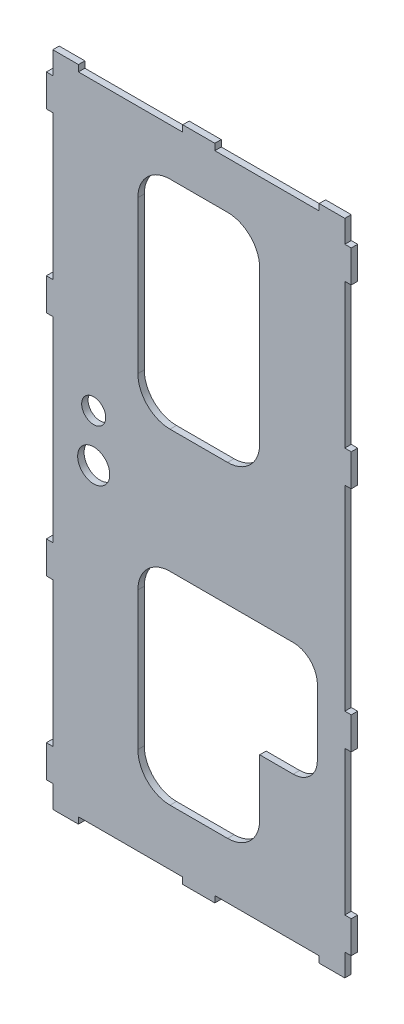
SolidWorks part; units mm, degrees
ref_plane "Front Plane" through (0, 0, 0) normal (0, 0, 1) x (1, 0, 0)
ref_plane "Top Plane" through (0, 0, 0) normal (0, 1, 0) x (1, 0, 0)
ref_plane "Right Plane" through (0, 0, 0) normal (1, 0, 0) x (0, 0, -1)
sketch "Sketch1" plane through (0, 0, 0) normal (0, 0, 1) x (1, 0, 0)
  line L0 (0, 263.7647) -> (0, -233.1278) construction
  line L2 (-75, -201) -> (-10, -201)
  line L3 (-95, -191) -> (-95, -171)
  line L5 (95, -191) -> (95, -171)
  line L10 (-95, 191) -> (-91, 191)
  line L11 (-91, 171) -> (-95, 171)
  line L12 (-95, 81) -> (-91, 81)
  line L13 (-91, 61) -> (-95, 61)
  line L14 (-95, -61) -> (-91, -61)
  line L15 (-91, -81) -> (-95, -81)
  line L16 (-95, -171) -> (-91, -171)
  line L17 (-91, -191) -> (-95, -191)
  line L18 (-91, 191) -> (-91, 205)
  line L19 (-95, 171) -> (-95, 191)
  line L20 (-91, 81) -> (-91, 171)
  line L21 (-95, 61) -> (-95, 81)
  line L22 (-91, -61) -> (-91, 61)
  line L23 (-95, -81) -> (-95, -61)
  line L24 (-91, -171) -> (-91, -81)
  line L26 (91, -191) -> (95, -191)
  line L27 (95, -171) -> (91, -171)
  line L28 (91, -171) -> (91, -81)
  line L29 (91, -81) -> (95, -81)
  line L30 (95, -61) -> (91, -61)
  line L31 (91, -61) -> (91, 61)
  line L32 (91, 61) -> (95, 61)
  line L33 (95, 81) -> (91, 81)
  line L34 (91, 81) -> (91, 171)
  line L35 (91, 171) -> (95, 171)
  line L36 (91, 191) -> (91, 205)
  line L37 (95, 191) -> (91, 191)
  line L38 (95, -81) -> (95, -61)
  line L39 (95, 61) -> (95, 81)
  line L40 (95, 171) -> (95, 191)
  line L41 (91, 205) -> (75, 205)
  line L43 (-75, 201) -> (-10, 201)
  line L46 (-75, 205) -> (-75, 201)
  line L47 (-10, 201) -> (-10, 205)
  line L48 (10, 205) -> (10, 201)
  line L49 (75, 201) -> (75, 205)
  line L51 (-75, 205) -> (-91, 205)
  line L53 (-91, 191) -> (-91, 205)
  line L55 (10, 201) -> (75, 201)
  line L56 (10, 205) -> (-10, 205)
  line L57 (0, 0) -> (175.3337, 0) construction
  line L58 (91, -205) -> (75, -205)
  line L59 (75, -201) -> (75, -205)
  line L60 (10, -205) -> (10, -201)
  line L61 (10, -205) -> (-10, -205)
  line L62 (-10, -201) -> (-10, -205)
  line L63 (-75, -205) -> (-75, -201)
  line L64 (-75, -205) -> (-91, -205)
  line L65 (10, -201) -> (75, -201)
  line L67 (-91, -191) -> (-91, -205)
  line L68 (91, -205) -> (91, -191)
  line L69 (-17.9491, 171.6978) -> (17.9491, 171.6978)
  line L70 (-37.9491, 151.6978) -> (-37.9491, 56.7417)
  line L71 (-17.9491, 36.7417) -> (17.9491, 36.7417)
  line L72 (37.9491, 151.6978) -> (37.9491, 56.7417)
  line L75 (-17.9491, -166.1801) -> (17.9491, -166.1801)
  line L76 (-37.9491, -146.1801) -> (-37.9491, -60)
  line L77 (-17.9491, -40) -> (17.9491, -40)
  line L78 (37.9491, -146.1801) -> (37.9491, -60)
  line L79 (-37.9491, -166.1801) -> (-32.6253, -159.7672) construction
  arc A0 (-17.9491, -166.1801) -> (-37.9491, -146.1801) centre (-17.9491, -146.1801) cw
  arc A1 (17.9491, -166.1801) -> (37.9491, -146.1801) centre (17.9491, -146.1801) ccw
  arc A2 (17.9491, -40) -> (37.9491, -60) centre (17.9491, -60) cw
  arc A3 (-37.9491, -60) -> (-17.9491, -40) centre (-17.9491, -60) cw
  arc A4 (-37.9491, 56.7417) -> (-17.9491, 36.7417) centre (-17.9491, 56.7417) ccw
  arc A5 (-17.9491, 171.6978) -> (-37.9491, 151.6978) centre (-17.9491, 151.6978) ccw
  arc A6 (17.9491, 36.7417) -> (37.9491, 56.7417) centre (17.9491, 56.7417) ccw
  arc A7 (17.9491, 171.6978) -> (37.9491, 151.6978) centre (17.9491, 151.6978) cw
  point P3 (0, 0)
  point P6 (-93, 191)
  point P7 (-93, -81)
  point P8 (0, -120.4673)
  point P66 (0, 122.6316)
  dimension "D1" = 20
  dimension "D2" = 190
  dimension "D3" = 410
  dimension "D4" = 14
  dimension "D5" = 14
  dimension "D6" = 20
  dimension "D7" = 20
  dimension "D8" = 90
  dimension "D9" = 20
  dimension "D10" = 90
  dimension "D11" = 20
extrude "Boss-Extrude2" add sketch "Sketch1" along normal blind 4
sketch "Sketch2" plane through (0, 0, 4) normal (0, 0, 1) x (1, 0, 0)
  line L0 (-17.9491, -40) -> (17.9491, -40) construction
  line L1 (0, -40) -> (58.8866, -40)
  line L2 (0, -40) -> (0, -111.045)
  line L3 (0, -111.045) -> (58.8866, -111.045)
  line L4 (73.8866, -55) -> (73.8866, -96.045)
  arc A0 (58.8866, -111.045) -> (73.8866, -96.045) centre (58.8866, -96.045) ccw
  arc A1 (58.8866, -40) -> (73.8866, -55) centre (58.8866, -55) cw
  point P6 (0, -40)
  dimension "D1" = 15
extrude "Cut-Extrude1" cut sketch "Sketch2" against normal blind 10
sketch "Sketch3" plane through (0, 0, 4) normal (0, 0, 1) x (1, 0, 0)
  circle A0 centre (-65.4973, 22.9167) radius 7.5
  circle A1 centre (-65.4973, -6.5835) radius 10
  dimension "D1" = 15
  dimension "D2" = 20
extrude "Cut-Extrude2" cut sketch "Sketch3" against normal blind 10
